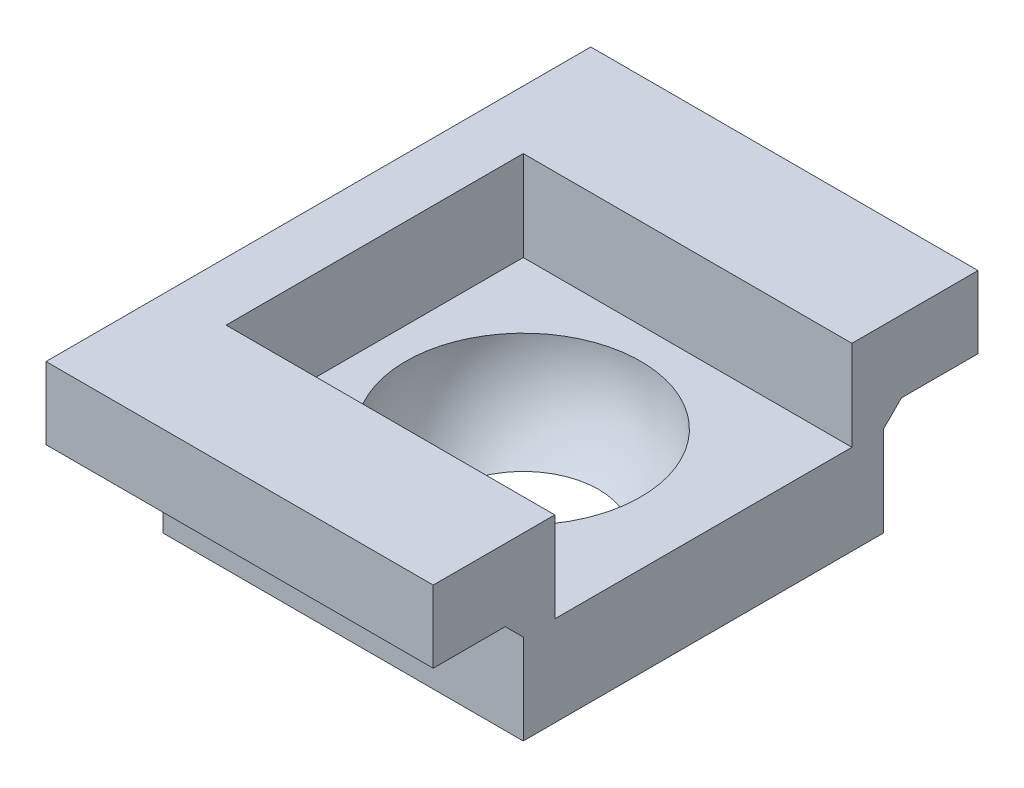
SolidWorks part; units mm, degrees
ref_plane "Front Plane" through (0, 0, 0) normal (0, 0, 1) x (1, 0, 0)
ref_plane "Top Plane" through (0, 0, 0) normal (0, 1, 0) x (1, 0, 0)
ref_plane "Right Plane" through (0, 0, 0) normal (1, 0, 0) x (0, 0, -1)
sketch "Sketch1" plane through (0, 0, 0) normal (0, 1, 0) x (1, 0, 0)
  line L1 (-2.306, 2.016) -> (1.694, 2.016)
  line L2 (-2.306, 2.016) -> (-2.306, -1.984)
  line L3 (-2.306, -1.984) -> (1.694, -1.984)
  line L4 (1.694, 2.016) -> (1.694, -1.984)
  dimension "D1" = 4
  dimension "D2" = 4
extrude "Boss-Extrude1" add sketch "Sketch1" along normal blind 2
sketch "Sketch2" plane through (0, 2, 0) normal (0, 1, 0) x (1, 0, 0)
  line L0 (1.694, 2.016) -> (-2.306, 2.016) construction
  line L1 (-2.306, 2.016) -> (-2.306, -1.984) construction
  line L2 (-0.306, -1.289) -> (-0.306, 1.321)
  arc A0 (-0.306, 1.321) -> (-0.306, -1.289) centre (-0.306, 0.016) ccw
  dimension "D3" = 2.61
  dimension "D1" = 2
  dimension "D2" = 2
revolve "Cut-Revolve1" cut sketch "Sketch2" angle 360 about L2
sketch "Sketch3" plane through (0, 0, 0) normal (0, -1, 0) x (1, 0, 0)
  line L1 (-4.7173, 2.6241) -> (2.2784, 2.6241)
  line L2 (-4.7173, 2.6241) -> (-4.7173, -2.1717)
  line L3 (-4.7173, -2.1717) -> (2.2784, -2.1717)
  line L4 (2.2784, 2.6241) -> (2.2784, -2.1717)
extrude "Cut-Extrude1" cut sketch "Sketch3" against normal blind 1
sketch "Sketch4" plane through (0, 2, 0) normal (0, 1, 0) x (1, 0, 0)
  line L0 (-2.306, -1.984) -> (1.694, -1.984) construction
  line L1 (-1.906, -1.584) -> (1.515, -1.584)
  line L2 (-1.906, -1.584) -> (-1.906, 1.616)
  line L3 (-1.906, 1.616) -> (1.515, 1.616)
  line L5 (1.694, 2.016) -> (-2.306, 2.016) construction
  line L6 (-2.306, 2.016) -> (-2.306, -1.984) construction
  line L7 (1.515, -1.584) -> (1.694, -1.584)
  line L8 (-2.306, -1.984) -> (1.694, -1.984)
  line L9 (-2.306, -1.984) -> (-2.306, 2.066)
  line L10 (-2.306, 2.066) -> (1.694, 2.066)
  line L11 (1.694, -1.984) -> (1.694, -1.584)
  line L12 (1.515, 1.616) -> (1.694, 1.616)
  line L13 (1.694, 1.616) -> (1.694, 2.066)
  dimension "D1" = 0.4
  dimension "D2" = 0.4
  dimension "D3" = 0.4
extrude "Boss-Extrude2" add sketch "Sketch4" along normal blind 1
sketch "Sketch5" plane through (0, 0, 1.984) normal (0, 0, 1) x (1, 0, 0)
  line L5 (1.694, 3) -> (1.694, 1) construction
  line L6 (-2.306, 3) -> (1.694, 3)
  line L7 (-2.306, 3) -> (-2.306, 2.2)
  line L8 (-2.306, 2.2) -> (1.694, 2.2)
  line L9 (1.694, 3) -> (1.694, 2.2)
  dimension "D1" = 0.8
extrude "Boss-Extrude3" add sketch "Sketch5" along normal blind 1
sketch "Sketch6" plane through (0, 0, -2.066) normal (0, 0, -1) x (-1, 0, 0)
  line L0 (2.306, 3) -> (2.306, 2) construction
  line L1 (-1.694, 3) -> (2.306, 3)
  line L2 (-1.694, 3) -> (-1.694, 2.2)
  line L3 (-1.694, 2.2) -> (2.306, 2.2)
  line L4 (2.306, 3) -> (2.306, 2.2)
  dimension "D1" = 0.8
extrude "Boss-Extrude4" add sketch "Sketch6" along normal blind 1
sketch "Sketch8" plane through (0, 2, 0) normal (0, -1, 0) x (1, 0, 0)
  line L1 (1.694, -2.066) -> (-2.306, -2.066)
  line L2 (1.694, -2.066) -> (1.694, -2.016)
  line L3 (1.694, -2.016) -> (-2.306, -2.016)
  line L4 (-2.306, -2.066) -> (-2.306, -2.016)
extrude "Cut-Extrude2" cut sketch "Sketch8" against normal up to surface (0.2 mm away) up to face at (-0.306, 2.2, -2.566)
sketch "Sketch9" plane through (-2.306, 0, 0) normal (-1, 0, 0) x (0, 0, 1)
  line L1 (-3.066, 3) -> (2.984, 3)
  line L2 (-3.066, 3) -> (-3.066, 2.2)
  line L3 (-3.066, 2.2) -> (2.984, 2.2)
  line L4 (2.984, 3) -> (2.984, 2.2)
extrude "Boss-Extrude6" add sketch "Sketch9" along normal blind 0.3
sketch "Sketch10" plane through (0, 3, 0) normal (0, 1, 0) x (1, 0, 0)
  line L0 (1.694, -1.584) -> (-1.906, -1.584) construction
  line L1 (-1.956, -1.634) -> (2.0958, -1.634)
  line L2 (-1.956, -1.634) -> (-1.956, 1.666)
  line L3 (-1.956, 1.666) -> (2.0958, 1.666)
  line L4 (2.0958, -1.634) -> (2.0958, 1.666)
  line L5 (-1.906, 1.616) -> (1.694, 1.616) construction
  line L6 (-1.906, -1.584) -> (-1.906, 1.616) construction
  dimension "D1" = 0.05
  dimension "D2" = 0.05
  dimension "D3" = 0.05
extrude "Cut-Extrude3" cut sketch "Sketch10" against normal up to surface (1 mm away) up to face at (-0.306, 2, 1.289)
sketch "Sketch11" plane through (1.694, 0, 0) normal (1, 0, 0) x (0, 0, -1)
  line L0 (-1.984, 2) -> (-2.184, 2.2)
  line L1 (-1.984, 2.2) -> (-1.984, 1) construction
  line L2 (-2.984, 2.2) -> (-1.984, 2.2) construction
  line L3 (-2.184, 2.2) -> (-1.984, 2.2)
  line L4 (-1.984, 2.2) -> (-1.984, 2)
  dimension "D1" = 0.2
  dimension "D2" = 0.2
extrude "Boss-Extrude7" add sketch "Sketch11" against normal up to surface (4 mm away) up to face at (-2.306, 1.6, -0.016)
sketch "Sketch12" plane through (1.694, 0, 0) normal (1, 0, 0) x (0, 0, -1)
  line L0 (2.016, 2.2) -> (2.016, 2)
  line L1 (2.016, 2.2) -> (2.016, 1) construction
  line L2 (2.016, 2) -> (2.216, 2.2)
  line L3 (3.066, 2.2) -> (2.016, 2.2) construction
  line L4 (2.216, 2.2) -> (2.016, 2.2)
  dimension "D1" = 0.2
  dimension "D2" = 0.2
extrude "Boss-Extrude8" add sketch "Sketch12" against normal up to surface (4 mm away) up to face at (-2.306, 1.68, 0.424)
